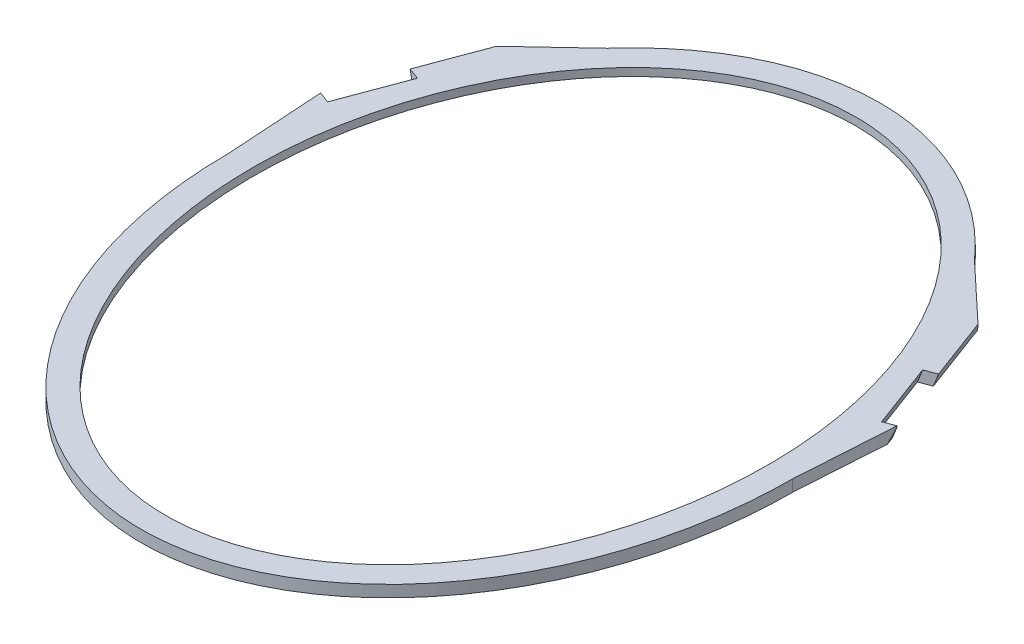
SolidWorks part; units mm, degrees
ref_plane "Front Plane" through (0, 0, 0) normal (0, 0, 1) x (1, 0, 0)
ref_plane "Top Plane" through (0, 0, 0) normal (0, 1, 0) x (1, 0, 0)
ref_plane "Right Plane" through (0, 0, 0) normal (1, 0, 0) x (0, 0, -1)
sketch "Sketch1" plane through (0, 0, 0) normal (0, 1, 0) x (1, 0, 0)
  line L0 (0, 520.2694) -> (0, -520.3963) construction
  ellipse E0 centre (0, 0) end of major axis (0, 355) minor radius 265
  ellipse E1 centre (0, 0) end of major axis (0, 380) minor radius 290
  dimension "D1" = 530
  dimension "D2" = 710
  dimension "D3" = 580
  dimension "D4" = 760
extrude "Boss-Extrude1" add sketch "Sketch1" along normal blind 12
sketch "Sketch2" plane through (0, 0, 0) normal (0, -1, 0) x (1, 0, 0)
  line L0 (0, -520.2694) -> (0, 520.3963) construction
  ellipse E0 centre (0, 0) end of major axis (0, 355) minor radius 265
  ellipse E2 centre (0, 0) end of major axis (0, 365) minor radius 275
  dimension "D1" = 10
  dimension "D2" = 10
extrude "Cut-Extrude1" cut sketch "Sketch2" against normal blind 4
sketch "Sketch4" plane through (0, 0, 0) normal (0, -1, 0) x (1, 0, 0)
  line L0 (-290, 0) -> (-295.5757, -86.6197)
  line L1 (-295.5757, -86.6197) -> (-301.7405, -182.3924)
  line L3 (-247.6321, -233.1808) -> (-240.894, -239.5054)
  line L4 (-240.894, -239.5054) -> (-188.9895, -288.2251)
  line L5 (-247.6321, -233.1808) -> (-301.7405, -182.3924)
  line L6 (-235.3988, -237.9079) -> (-188.9895, -288.2251) construction
  line L8 (-188.9895, -288.2251) -> (-243.259, -170.233)
  line L9 (0, 0) -> (0, -412.1896) construction
  line L10 (-243.259, -170.233) -> (-265.308, -122.2944)
  line L11 (-265.308, -122.2944) -> (-290, 0)
  ellipse E1 centre (0, 0) end of major axis (0, -380) minor radius 290 construction
  ellipse E2 centre (0, 0) end of major axis (0, 365) minor radius 275 construction
extrude "Boss-Extrude2" add sketch "Sketch4" against normal blind 12
ref_plane "Plane1" through (-258.2545, -96.3551, -96.3551) normal (-0.8844, -0.33, -0.33) x (-0.3092, -0.1154, 0.944)
sketch "Sketch5" plane through (-258.2545, -96.3551, -96.3551) normal (-0.8844, -0.33, -0.33) x (-0.3092, -0.1154, 0.944)
  line L1 (-239.4181, 192.9721) -> (70.1119, 192.9721)
  line L2 (-239.4181, 192.9721) -> (-239.4181, 21.3)
  line L3 (-239.4181, 21.3) -> (70.1119, 21.3)
  line L4 (70.1119, 192.9721) -> (70.1119, 21.3)
extrude "Cut-Extrude2" cut sketch "Sketch5" along normal through all
sketch "Sketch6" plane through (-258.2545, -96.3551, -96.3551) normal (-0.8844, -0.33, -0.33) x (-0.3092, -0.1154, 0.944)
  line L0 (-30.8651, 131.7856) -> (-7.176, 131.7856)
  line L4 (-7.176, 131.7856) -> (-4.5847, 110.7382)
  line L21 (-173.6702, 233.3063) -> (-220.8716, 228.0255)
  line L22 (-401.7678, 135.9252) -> (-418.1252, 117.4304)
  line L23 (-418.1252, 117.4304) -> (-427.114, 125.3804)
  line L24 (-427.114, 125.3804) -> (-657.9638, -135.634)
  line L25 (-657.9638, -135.634) -> (-650.4731, -142.2589)
  line L26 (-650.4731, -142.2589) -> (-658.4988, -151.3333)
  line L27 (-658.4988, -151.3333) -> (-651.0082, -157.9583)
  line L28 (-651.0082, -157.9583) -> (-642.9825, -148.8839)
  line L29 (-642.9825, -148.8839) -> (-635.4918, -155.5089)
  line L30 (-635.4918, -155.5089) -> (-643.5175, -164.5833)
  line L31 (-643.5175, -164.5833) -> (-636.0269, -171.2082)
  line L32 (-636.0269, -171.2082) -> (-537.8686, -60.2239)
  line L33 (-144.9445, 97.806) -> (-76.4006, 106.245)
  line L34 (-76.4006, 106.245) -> (-73.2939, 81.0114)
  line L35 (-73.2939, 81.0114) -> (-2.0054, 89.7883)
  line L36 (-2.0054, 89.7883) -> (-4.5847, 110.7382)
  line L37 (-4.5847, 110.7382) -> (-30.8651, 131.7856)
  line L38 (-173.6702, 233.3063) -> (-220.8716, 228.0255)
  line L39 (-401.7678, 135.9252) -> (-418.1252, 117.4304)
  line L40 (-418.1252, 117.4304) -> (-427.114, 125.3804)
  line L41 (-427.114, 125.3804) -> (-657.9638, -135.634)
  line L42 (-657.9638, -135.634) -> (-650.4731, -142.2589)
  line L43 (-650.4731, -142.2589) -> (-658.4988, -151.3333)
  line L44 (-658.4988, -151.3333) -> (-651.0082, -157.9583)
  line L45 (-651.0082, -157.9583) -> (-642.9825, -148.8839)
  line L46 (-642.9825, -148.8839) -> (-635.4918, -155.5089)
  line L47 (-635.4918, -155.5089) -> (-643.5175, -164.5833)
  line L48 (-643.5175, -164.5833) -> (-636.0269, -171.2082)
  line L49 (-636.0269, -171.2082) -> (-537.8686, -60.2239)
  line L50 (-144.9445, 97.806) -> (-76.4006, 106.245)
  line L51 (-76.4006, 106.245) -> (-73.2939, 81.0114)
  line L52 (-73.2939, 81.0114) -> (-2.0054, 89.7883)
  line L53 (-2.0054, 89.7883) -> (-4.5847, 110.7382)
  parabola Q2 (-54.4692, 127.3111) -> (-173.6702, 233.3063) focus (-75.4374, 170.8375) apex (-87.2988, 130.4611)
  parabola Q3 (-220.8716, 228.0255) -> (-283.0266, 171.8338) focus (-305.1764, 265.4008) apex (-242.4046, 202.2046)
  parabola Q4 (-54.4692, 127.3111) -> (-173.6702, 233.3063) focus (-75.4374, 170.8375) apex (-87.2988, 130.4611)
  parabola Q5 (-220.8716, 228.0255) -> (-283.0266, 171.8338) focus (-305.1764, 265.4008) apex (-242.4046, 202.2046)
  spline S4 degree 3 poles (-1892.4602, 2613.4419) (2441.7292, -1720.4512) (-3312.8242, 1868.517) (1866.524, -1857.1401) knots -4.743421 -4.743421 -4.743421 -4.743421 7.38584 7.38584 7.38584 7.38584 only from (-283.0266, 171.8338) to (-289.7687, 168.4955)
  spline S5 degree 3 poles (-54.5903, -2757.6254) (444.4417, 3955.6459) (-381.6681, -3336.2626) (-1450.7779, 2883.8504) knots -4.479462 -4.479462 -4.479462 -4.479462 3.398029 3.398029 3.398029 3.398029 only from (-289.7687, 168.4955) to (-401.7678, 135.9252)
  spline S6 degree 3 poles (-1556.5784, 2726.4387) (-661.4955, -1063.4918) (-718.1632, -13.7802) (-117.5723, 178.8561) (206.7014, 119.123) (-764.4496, -2818.6457) knots -1.959297 -1.959297 -1.959297 -1.959297 0.468078 0.643593 2.020972 2.020972 2.020972 2.020972 only from (-537.8686, -60.2239) to (-144.9445, 97.806)
  spline S7 degree 3 poles (-30.8651, 131.7856) (-37.7808, 129.0257) (-45.6847, 127.4087) (-54.4692, 127.3111) knots 0.075373 0.075373 0.075373 0.075373 0.225516 0.225516 0.225516 0.225516 weights 1 0.918164 0.848615 0.791353
  spline S8 degree 3 poles (-283.0266, 171.8338) (-285.2701, 170.7062) (-287.5181, 169.5939) (-289.7687, 168.4955) knots 0.946107 0.946107 0.946107 0.946107 1 1 1 1
  spline S9 degree 3 poles (-289.7687, 168.4955) (-325.1106, 151.4823) (-362.4995, 139.205) (-401.7678, 135.9252) knots 0 0 0 0 0.423036 0.423036 0.423036 0.423036
  spline S10 degree 3 poles (-537.8686, -60.2239) (-492.1571, -6.5784) (-422.5209, 81.0455) (-274.3864, 128.5588) (-187.0397, 138.6603) (-144.9445, 97.806) knots 0 0 0 0 0.468078 0.643593 0.981724 0.981724 0.981724 0.981724
  spline S11 degree 3 poles (-30.8651, 131.7856) (-37.7808, 129.0257) (-45.6847, 127.4087) (-54.4692, 127.3111) knots 0.075373 0.075373 0.075373 0.075373 0.225516 0.225516 0.225516 0.225516 weights 1 0.918164 0.848615 0.791353
  dimension "D1" = 0
extrude "Cut-Extrude3" cut sketch "Sketch6" against normal blind 12
mirror "Mirror1" about plane through (0, 0, 0) normal (1, 0, 0) of "Cut-Extrude3", "Cut-Extrude2", "Boss-Extrude2"
sketch "Sketch7" plane through (0, 12, 0) normal (0, 1, 0) x (1, 0, 0)
  line L0 (0, -500) -> (0, 500)
  arc A0 (0, 500) -> (0, -500) centre (0, 0) cw
  dimension "D1" = 500
extrude "Cut-Extrude4" [suppressed] cut sketch "Sketch7" against normal blind 12
sketch "Sketch8" plane through (0, 12, 0) normal (0, 1, 0) x (1, 0, 0)
  line L0 (0, -500) -> (0, 500)
  arc A0 (0, -500) -> (0, 500) centre (0, 0) cw
  dimension "D1" = 500
extrude "Cut-Extrude5" [suppressed] cut sketch "Sketch8" against normal blind 12
